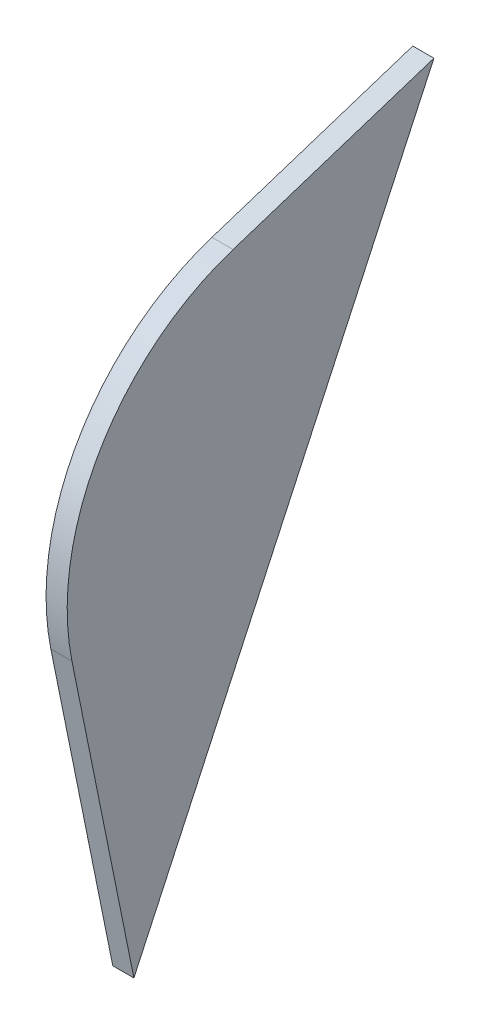
SolidWorks part; units mm, degrees
ref_plane "Alzado" through (0, 0, 0) normal (0, 0, 1) x (1, 0, 0)
ref_plane "Planta" through (0, 0, 0) normal (0, 1, 0) x (1, 0, 0)
ref_plane "Vista lateral" through (0, 0, 0) normal (1, 0, 0) x (0, 0, -1)
sketch "Croquis1" plane through (0, 0, 0) normal (1, 0, 0) x (0, 0, -1)
  line L0 (8.7852, 25.5181) -> (37.3175, 34.7869)
  line L1 (-5.3032, -57.0602) -> (-14.0987, -13.6906)
  line L2 (37.3175, 34.7869) -> (-5.3032, -57.0602)
  arc A0 (8.7852, 25.5181) -> (-14.0987, -13.6906) centre (19.3205, -6.9131) ccw
extrude "Saliente-Extruir1" add sketch "Croquis1" along normal blind 3
